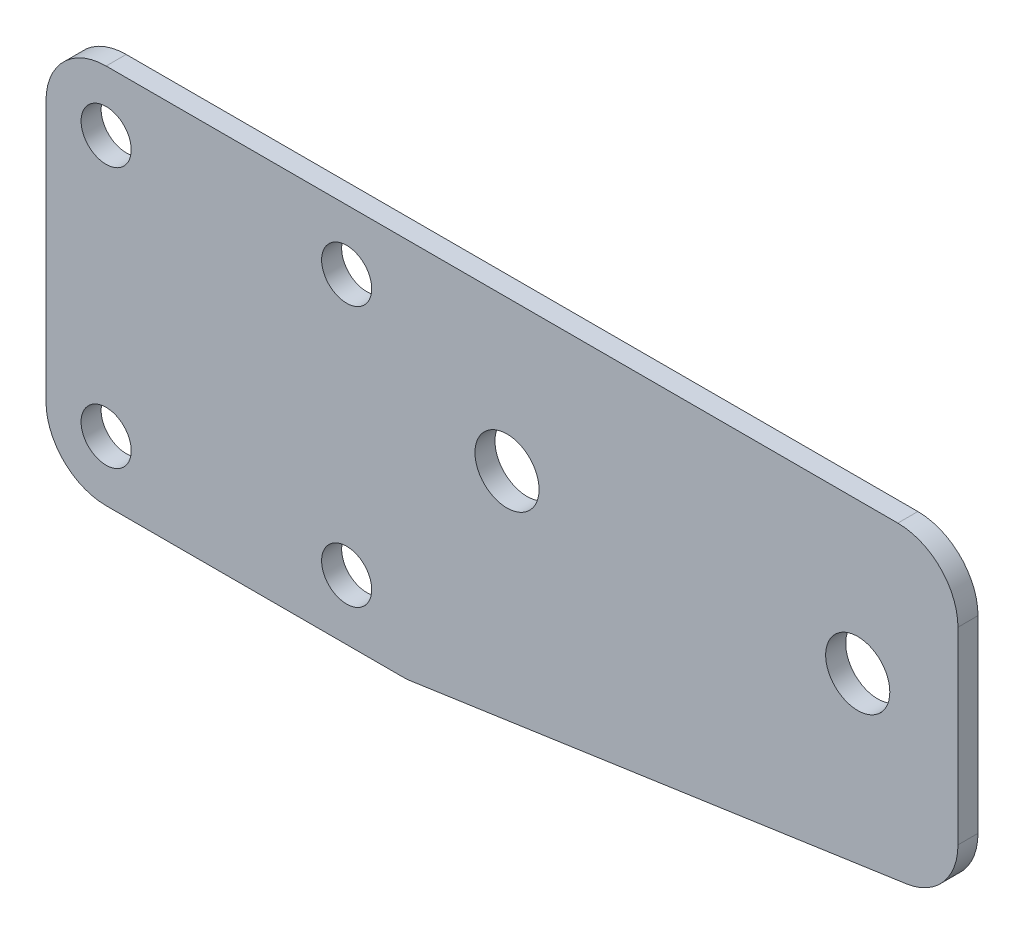
SolidWorks part; units mm, degrees
ref_plane "Plano frontal" through (0, 0, 0) normal (0, 0, 1) x (1, 0, 0)
ref_plane "Plano superior" through (0, 0, 0) normal (0, 1, 0) x (1, 0, 0)
ref_plane "Plano direito" through (0, 0, 0) normal (1, 0, 0) x (0, 0, -1)
sketch "Esboço1" plane through (0, 0, 0) normal (0, 0, 1) x (1, 0, 0)
  line L0 (0, 11.75) -> (0, 0) construction
  line L1 (-9, 9.5) -> (9, 9.5)
  line L2 (-9, 9.5) -> (-9, -9.5)
  line L3 (-9, -9.5) -> (9, -9.5)
  line L4 (9, 9.5) -> (9, -9.5) construction
  line L5 (-9, 9.5) -> (9, -9.5) construction
  line L6 (-9, -9.5) -> (9, 9.5) construction
  line L7 (0, 0) -> (7.3285, 0) construction
  line L8 (9, 9.5) -> (36.5, 9.5)
  line L9 (36.5, 9.5) -> (36.5, -5.5)
  line L10 (36.5, -5.5) -> (9, -9.5)
  line L11 (36.5, 2) -> (13.2423, 2) construction
  line L12 (22.75, 9.5) -> (22.75, -2.0211) construction
  circle A0 centre (6, -6.5) radius 1.25
  circle A1 centre (6, 6.5) radius 1.25
  circle A2 centre (-6, -6.5) radius 1.25
  circle A3 centre (-6, 6.5) radius 1.25
  circle A4 centre (-6, 6.5) radius 3 construction
  circle A5 centre (31.5, 2) radius 1.6
  circle A6 centre (14, 2) radius 1.6
  point P0 (0, 0)
  dimension "D1" = 2.5
  dimension "D4" = 6
  dimension "D7" = 3.2
  dimension "D2" = 13
  dimension "D3" = 12
  dimension "D5" = 27.5
  dimension "D6" = 15
  dimension "D8" = 5
extrude "Ressalto-extrusão1" add sketch "Esboço1" along normal blind 1
fillet "Filete1" radius 3 5 edges at (9, -9.5, 0.5) (36.5, -5.5, 0.5) (36.5, 9.5, 0.5) (-9, -9.5, 0.5) (-9, 9.5, 0.5)
